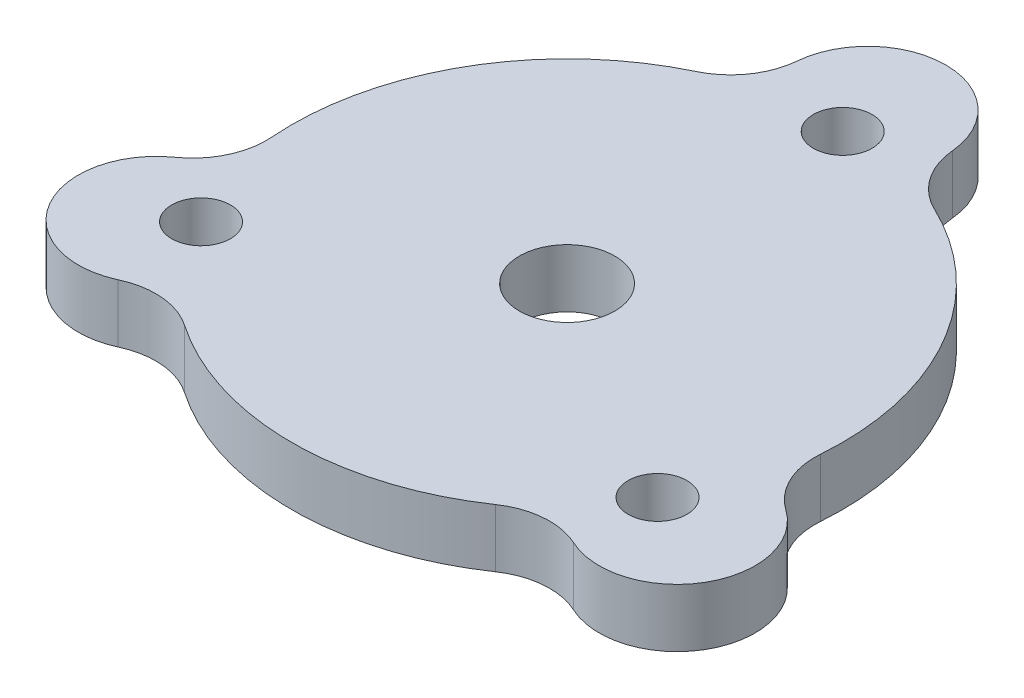
SolidWorks part; units mm, degrees
material "Acrylic (Medium-high impact)"
ref_plane "Front" through (0, 0, 0) normal (0, 0, 1) x (1, 0, 0)
ref_plane "Top" through (0, 0, 0) normal (0, 1, 0) x (1, 0, 0)
ref_plane "Right" through (0, 0, 0) normal (1, 0, 0) x (0, 0, -1)
sketch "Sketch1" plane through (0, 0, 0) normal (0, 1, 0) x (1, 0, 0)
  line L0 (-4.25, 16.3853) -> (-4.25, 14.3853)
  line L1 (4.25, 16.3853) -> (4.25, 14.3853)
  line L2 (0, 28.2076) -> (0, 14.0098) construction
  line L3 (0, 2.6) -> (0, -26.1578) construction
  line L4 (16.3151, -4.5121) -> (14.5831, -3.5121)
  line L5 (12.0651, -11.8733) -> (10.3331, -10.8733)
  line L6 (-12.0651, -11.8733) -> (-10.3331, -10.8733)
  line L7 (-16.3151, -4.5121) -> (-14.5831, -3.5121)
  circle A0 centre (0, 0) radius 2.6
  arc A1 (-4.25, 14.3853) -> (-14.5831, -3.5121) centre (0, 0) ccw
  arc A2 (-4.25, 16.3853) -> (4.25, 16.3853) centre (0, 16.3853) cw
  arc A3 (16.3151, -4.5121) -> (12.0651, -11.8733) centre (14.1901, -8.1927) cw
  arc A4 (-12.0651, -11.8733) -> (-16.3151, -4.5121) centre (-14.1901, -8.1927) cw
  arc A5 (-10.3331, -10.8733) -> (10.3331, -10.8733) centre (0, 0) ccw
  arc A6 (14.5831, -3.5121) -> (4.25, 14.3853) centre (0, 0) ccw
  dimension "D1" = 5.2
  dimension "D2" = 30
  dimension "D3" = 8.5
  dimension "D4" = 2
  dimension "D5" = 3
extrude "Boss-Extrude1" add sketch "Sketch1" along normal blind 3.175
fillet "Fillet1" radius 4 6 edges at (-14.5831, 1.5875, 3.5121) (-4.25, 1.5875, -14.3853) (4.25, 1.5875, -14.3853) (14.5831, 1.5875, 3.5121) (10.3331, 1.5875, 10.8733) (-10.3331, 1.5875, 10.8733)
sketch "Sketch2" plane through (0, 3.175, 0) normal (0, 1, 0) x (1, 0, 0)
  circle A0 centre (-12.885, -7.0593) radius 1.6 construction
  circle A1 centre (12.556, -7.6291) radius 1.6 construction
  circle A2 centre (0.329, 14.6884) radius 1.6 construction
  circle A3 centre (-12.885, -7.0593) radius 1.6
  circle A4 centre (12.556, -7.6291) radius 1.6
  circle A5 centre (0.329, 14.6884) radius 1.6
extrude "Cut-Extrude1" cut sketch "Sketch2" against normal through all
